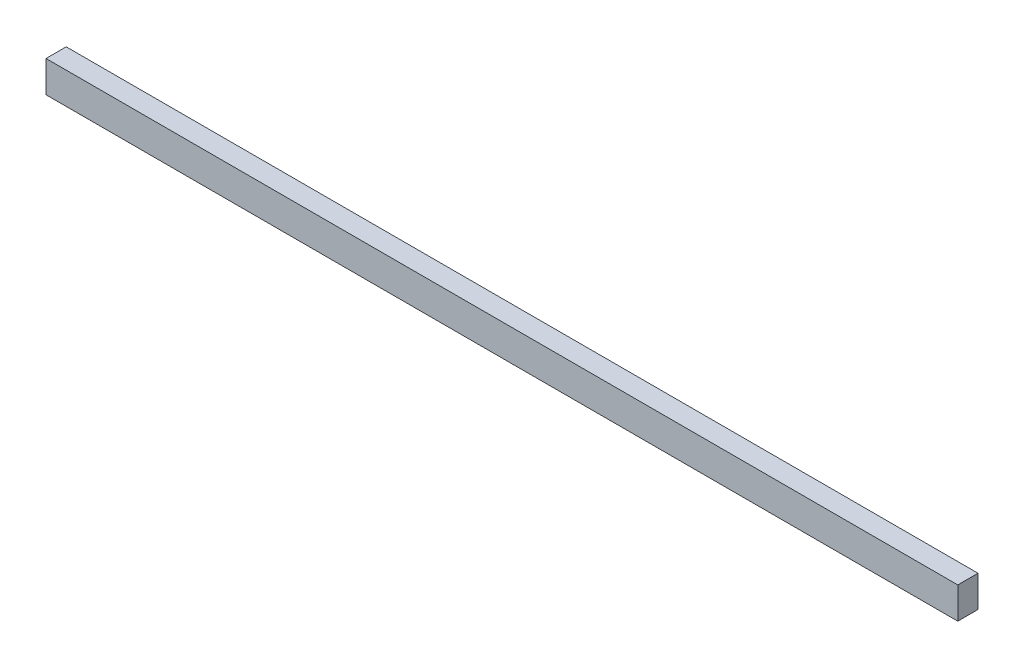
SolidWorks part; units mm, degrees
material "Pine"
ref_plane "Front Plane" through (0, 0, 0) normal (0, 0, 1) x (1, 0, 0)
ref_plane "Top Plane" through (0, 0, 0) normal (0, 1, 0) x (1, 0, 0)
ref_plane "Right Plane" through (0, 0, 0) normal (1, 0, 0) x (0, 0, -1)
sketch "Sketch1" plane through (0, 0, 0) normal (1, 0, 0) x (0, 0, -1)
  line L1 (0, 0) -> (45, 0)
  line L2 (0, 0) -> (0, 70)
  line L3 (0, 70) -> (45, 70)
  line L4 (45, 0) -> (45, 70)
  dimension "D1" = 70
  dimension "D2" = 45
extrude "Boss-Extrude1" add sketch "Sketch1" along normal blind 2030
